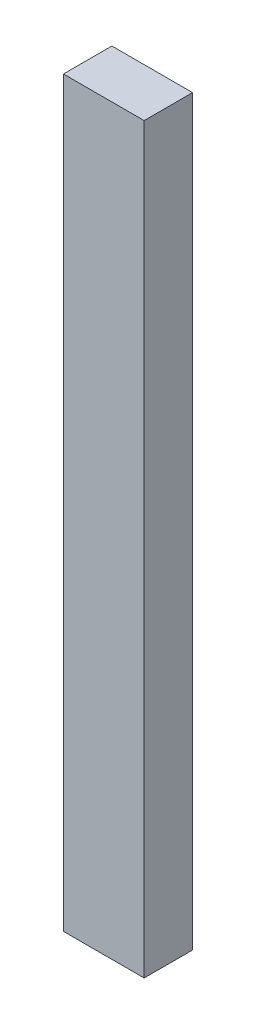
SolidWorks part; units mm, degrees
material "1060-H16"
ref_plane "Front Plane" through (0, 0, 0) normal (0, 0, 1) x (1, 0, 0)
ref_plane "Top Plane" through (0, 0, 0) normal (0, 1, 0) x (1, 0, 0)
ref_plane "Right Plane" through (0, 0, 0) normal (1, 0, 0) x (0, 0, -1)
sketch "Sketch1" plane through (0, 0, 0) normal (0, 1, 0) x (1, 0, 0)
  line L1 (-0.25, 0.15) -> (0.25, 0.15)
  line L2 (-0.25, 0.15) -> (-0.25, -0.15)
  line L3 (-0.25, -0.15) -> (0.25, -0.15)
  line L4 (0.25, 0.15) -> (0.25, -0.15)
  line L5 (-0.25, 0.15) -> (0.25, -0.15) construction
  line L6 (-0.25, -0.15) -> (0.25, 0.15) construction
  point P0 (0, 0)
  dimension "D1" = 0.5
  dimension "D2" = 0.3
extrude "Boss-Extrude1" add sketch "Sketch1" along normal blind 4.6
